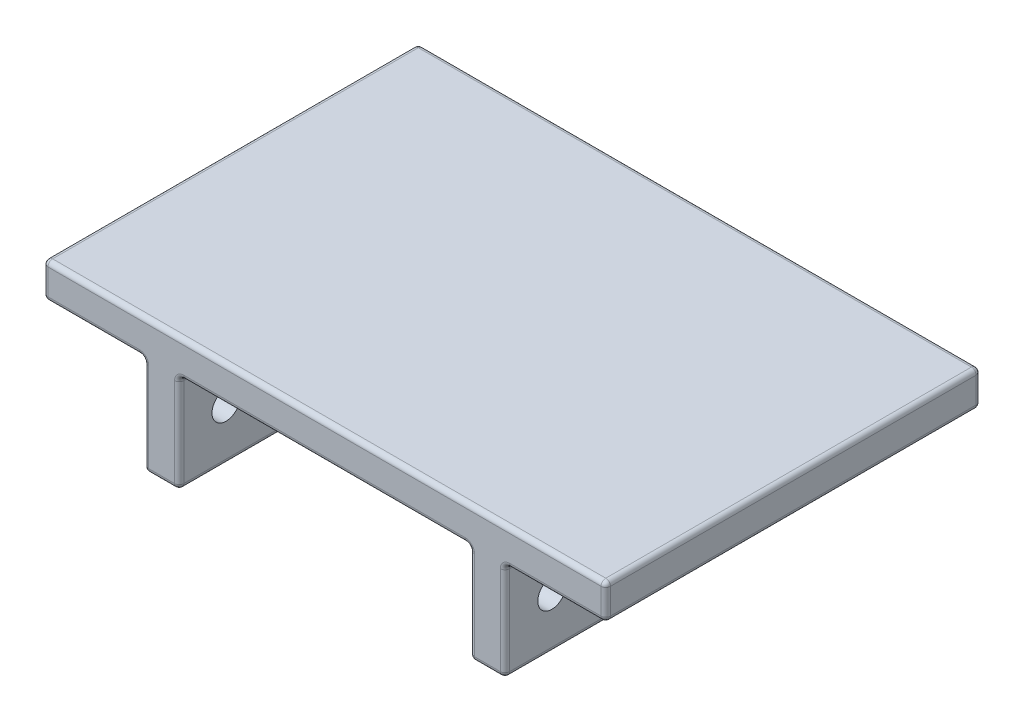
SolidWorks part; units mm, degrees
ref_plane "Front Plane" through (0, 0, 0) normal (0, 0, 1) x (1, 0, 0)
ref_plane "Top Plane" through (0, 0, 0) normal (0, 1, 0) x (1, 0, 0)
ref_plane "Right Plane" through (0, 0, 0) normal (1, 0, 0) x (0, 0, -1)
sketch "Sketch1" plane through (0, 0, 0) normal (0, 1, 0) x (1, 0, 0)
  line L1 (-76.2, 50.8) -> (76.2, 50.8)
  line L2 (-76.2, 50.8) -> (-76.2, -50.8)
  line L3 (-76.2, -50.8) -> (76.2, -50.8)
  line L4 (76.2, 50.8) -> (76.2, -50.8)
  line L5 (-76.2, 50.8) -> (76.2, -50.8) construction
  line L6 (-76.2, -50.8) -> (76.2, 50.8) construction
  point P0 (0, 0)
  dimension "D1" = 152.4
  dimension "D2" = 101.6
extrude "Boss-Extrude1" add sketch "Sketch1" against normal blind 9.525
sketch "Sketch2" plane through (0, -9.525, 0) normal (0, -1, 0) x (1, 0, 0)
  line L0 (39.37, 50.8) -> (48.895, 50.8)
  line L1 (-48.895, 50.8) -> (-39.37, 50.8)
  line L2 (-48.895, 50.8) -> (-48.895, -50.8)
  line L3 (-48.895, -50.8) -> (-39.37, -50.8)
  line L4 (48.895, 50.8) -> (48.895, -50.8)
  line L5 (-48.895, 50.8) -> (48.895, -50.8) construction
  line L6 (-48.895, -50.8) -> (48.895, 50.8) construction
  line L7 (-48.895, 50.8) -> (-39.37, 50.8)
  line L8 (-48.895, 50.8) -> (-48.895, -50.8)
  line L9 (-48.895, -50.8) -> (-39.37, -50.8)
  line L10 (-39.37, 50.8) -> (-39.37, -50.8)
  line L11 (48.895, 50.8) -> (39.37, 50.8)
  line L12 (48.895, 50.8) -> (48.895, -50.8)
  line L13 (48.895, -50.8) -> (39.37, -50.8)
  line L14 (39.37, 50.8) -> (39.37, -50.8)
  line L15 (39.37, -50.8) -> (48.895, -50.8)
  point P0 (0, 0)
  line M6 (76.2, 50.8) -> (-76.2, 50.8)
  line M8 (-76.2, -50.8) -> (76.2, -50.8)
  dimension "D1" = 97.79
  dimension "D2" = 101.6
  dimension "D3" = 9.525
  dimension "D4" = 9.525
extrude "Boss-Extrude2" add sketch "Sketch2" along normal blind 26.67 contours L10 L2 M6 M8 | L14 L4 M6 M8
fillet "Fillet1" radius 1.27 36 edges at (39.37, -22.86, -50.8) (39.37, -22.86, 50.8) (-62.5475, -9.525, -50.8) (62.5475, -9.525, -50.8) (0, -9.525, -50.8) (-48.895, -22.86, -50.8) (-48.895, -22.86, 50.8) (-48.895, -9.525, 0) (62.5475, -9.525, 50.8) (0, -9.525, 50.8) (-62.5475, -9.525, 50.8) (0, 0, 50.8) (76.2, -4.7625, -50.8) (76.2, -9.525, 0) (76.2, -4.7625, 50.8) (76.2, 0, 0) (48.895, -22.86, 50.8) (48.895, -22.86, -50.8) (48.895, -9.525, 0) (48.895, -36.195, 0) (44.1325, -36.195, 50.8) (44.1325, -36.195, -50.8) (39.37, -36.195, 0) (-39.37, -22.86, 50.8) (-39.37, -22.86, -50.8) (-39.37, -9.525, 0) (-44.1325, -36.195, 50.8) (-44.1325, -36.195, -50.8) (-48.895, -36.195, 0) (-39.37, -36.195, 0) (-76.2, -4.7625, 50.8) (-76.2, -9.525, 0) (-76.2, -4.7625, -50.8) (-76.2, 0, 0) (39.37, -9.525, 0) (0, 0, -50.8)
sketch "Sketch3" plane through (-48.895, 0, 0) normal (-1, 0, 0) x (0, 0, 1)
  line L0 (50.8, -10.795) -> (50.8, -34.925) construction
  line L1 (-50.8, -34.925) -> (-50.8, -10.795) construction
  line L2 (49.53, -9.525) -> (-49.53, -9.525) construction
  circle A0 centre (12.7, -22.225) radius 3.81
  circle A1 centre (38.1, -22.225) radius 3.81
  circle A2 centre (-38.1, -22.225) radius 3.81
  circle A3 centre (-12.7, -22.225) radius 3.81
  point P4 (25.9162, -22.1517)
  point P11 (9.0596, -14.1717)
  dimension "D1" = 7.62
  dimension "D2" = 7.62
  dimension "D4" = 7.62
  dimension "D5" = 7.62
  dimension "D3" = 25.4
  dimension "D6" = 25.4
  dimension "D7" = 12.7
  dimension "D8" = 12.7
  dimension "D9" = 12.7
extrude "Cut-Extrude1" cut sketch "Sketch3" against normal through all
